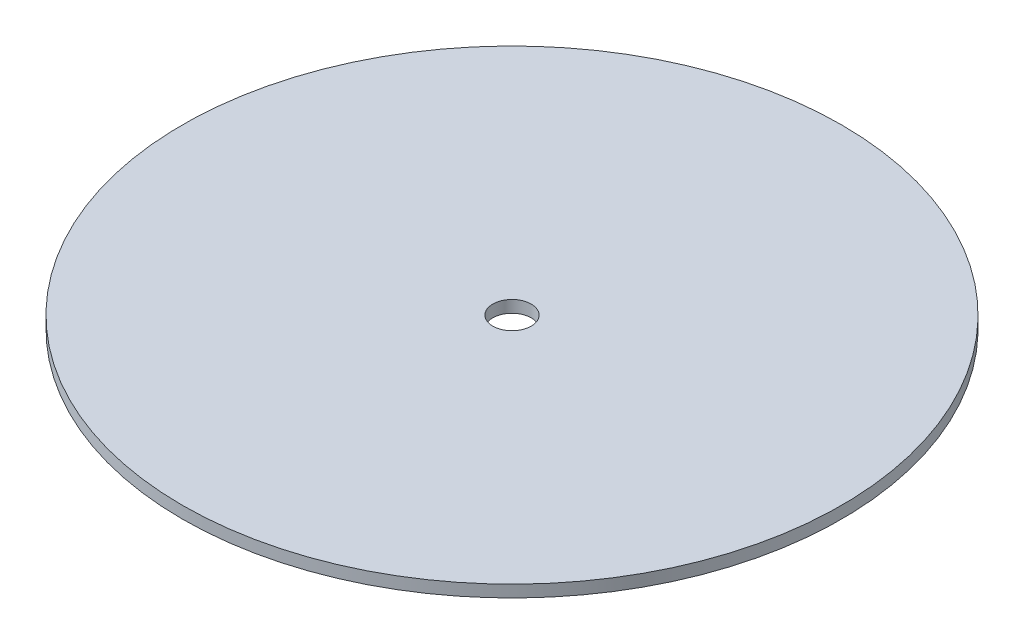
SolidWorks part; units mm, degrees
ref_plane "Front Plane" through (0, 0, 0) normal (0, 0, 1) x (1, 0, 0)
ref_plane "Top Plane" through (0, 0, 0) normal (0, 1, 0) x (1, 0, 0)
ref_plane "Right Plane" through (0, 0, 0) normal (1, 0, 0) x (0, 0, -1)
sketch "Sketch1" plane through (0, 0, 0) normal (0, 1, 0) x (1, 0, 0)
  circle A0 centre (0, 0) radius 137.5
  dimension "D1" = 275
extrude "Boss-Extrude1" add sketch "Sketch1" along normal blind 5
sketch "Sketch2" plane through (0, 5, 0) normal (0, 1, 0) x (1, 0, 0)
  circle A0 centre (0, 0) radius 8
  dimension "D1" = 16
extrude "Cut-Extrude1" cut sketch "Sketch2" against normal through all
